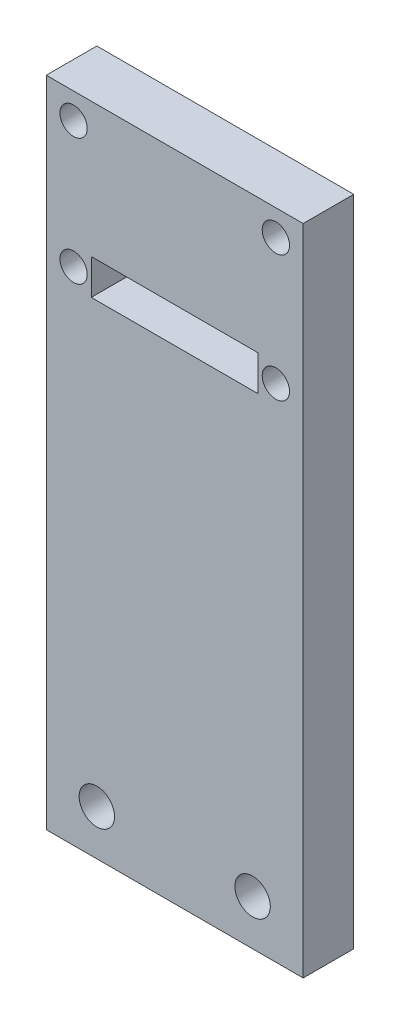
SolidWorks part; units mm, degrees
ref_plane "Front Plane" through (0, 0, 0) normal (0, 0, 1) x (1, 0, 0)
ref_plane "Top Plane" through (0, 0, 0) normal (0, 1, 0) x (1, 0, 0)
ref_plane "Right Plane" through (0, 0, 0) normal (1, 0, 0) x (0, 0, -1)
sketch "Sketch1" plane through (0, 0, 0) normal (0, 0, 1) x (1, 0, 0)
  line L0 (0, 154.6) -> (0, 127) construction
  line L1 (-12.7, 90) -> (12.7, 90)
  line L2 (-12.7, 90) -> (-12.7, 154.6)
  line L4 (12.7, 90) -> (12.7, 154.6)
  line L5 (0, 100) -> (0, 90) construction
  line L6 (0.1244, 127) -> (-0.4693, 127) construction
  line L8 (12.7, 154.6) -> (-12.7, 154.6)
  arc A5 (12.9, 99.1645) -> (-12.9, 99.1645) centre (0, 0) ccw construction
  dimension "D1" = 10
  dimension "D2" = 27.6
  dimension "D3" = 25.4
extrude "Boss-Extrude1" add sketch "Sketch1" against normal blind 5
sketch "Sketch2" plane through (0, 0, -5) normal (0, 0, -1) x (-1, 0, 0)
  line L0 (-12.7, 137) -> (12.7, 137) construction
  line L1 (-12.7, 90) -> (-12.7, 154.6) construction
  line L2 (12.7, 154.6) -> (12.7, 90) construction
  line L3 (-12.7, 154.6) -> (12.7, 154.6) construction
  line L4 (-12.7, 137) -> (-12.7, 154.6) construction
  line L5 (-12.7, 154.6) -> (12.7, 154.6) construction
  line L6 (12.7, 154.6) -> (12.7, 137) construction
  line L11 (-10, 139.55) -> (-10, 152.05) construction
  line L12 (-10, 152.05) -> (10, 152.05) construction
  line L13 (10, 152.05) -> (10, 139.55) construction
  line L14 (10, 139.55) -> (-10, 139.55) construction
  line L15 (0, 154.6) -> (0, 137) construction
  line L16 (-12.7, 145.8) -> (12.7, 145.8) construction
  line L18 (-8.25, 141.3) -> (8.25, 141.3)
  line L19 (-8.25, 141.3) -> (-8.25, 137.8)
  line L20 (-8.25, 137.8) -> (8.25, 137.8)
  line L21 (8.25, 141.3) -> (8.25, 137.8)
  circle A0 centre (-10, 152.05) radius 1.35
  circle A1 centre (10, 152.05) radius 1.35
  circle A2 centre (-10, 139.55) radius 1.35
  circle A3 centre (10, 139.55) radius 1.35
  point P18 (0, 139.55)
  point P21 (-10, 145.8)
  point P30 (0, 141.3)
  point P31 (-8.25, 139.55)
  dimension "D4" = 2.7
  dimension "D5" = 2.7
  dimension "D6" = 2.7
  dimension "D7" = 2.7
  dimension "D1" = 17.6
  dimension "D2" = 20
  dimension "D3" = 12.5
  dimension "D8" = 3.5
  dimension "D9" = 16.5
extrude "Cut-Extrude1" cut sketch "Sketch2" against normal through all
sketch "Sketch3" plane through (0, 0, 0) normal (0, 0, 1) x (1, 0, 0)
  line L0 (-12.9, 94.4822) -> (12.9, 94.4822) construction
  line L1 (-12.9, 99.1645) -> (-12.9, 89.8) construction
  line L2 (12.9, 89.8) -> (12.9, 99.1645) construction
  line L3 (0, 90) -> (0, 108.6126) construction
  line L4 (-12.7, 90) -> (12.7, 90) construction
  line L5 (-12.7, 154.6) -> (-12.7, 90) construction
  circle A0 centre (-7.7, 94.4822) radius 1.75
  circle A1 centre (7.7, 94.4822) radius 1.75
  dimension "D2" = 3.5
  dimension "D1" = 5
extrude "Cut-Extrude2" cut sketch "Sketch3" against normal through all
